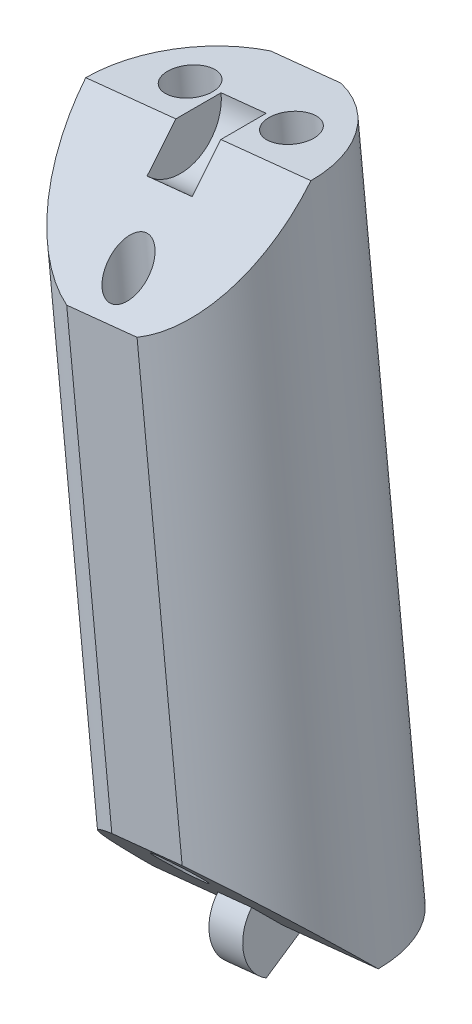
SolidWorks part; units mm, degrees
ref_plane "Front Plane" through (0, 0, 0) normal (0, 0, 1) x (1, 0, 0)
ref_plane "Top Plane" through (0, 0, 0) normal (0, 1, 0) x (1, 0, 0)
ref_plane "Right Plane" through (0, 0, 0) normal (1, 0, 0) x (0, 0, -1)
sketch "Sketch2" plane through (0, 0, 0) normal (0, 0, 1) x (1, 0, 0)
  line L0 (0, 0) -> (90, 0)
  line L1 (90, 0) -> (90, 120)
  line L2 (90, 120) -> (0, 120)
  line L3 (0, 120) -> (0, 0)
  line L4 (0, 120) -> (-10, 120)
  line L5 (-10, 120) -> (-10, 16.9491)
  line L6 (-10, 120) -> (57.5, 127)
  line L7 (57.5, 127) -> (90, 124)
  line L8 (90, 120) -> (99, 60)
  line L10 (90, 124) -> (90, 120)
  line L11 (5.9147, 0) -> (5.9147, -25)
  line L12 (5.9147, -25) -> (-4.0853, -25)
  line L13 (-4.0853, -29) -> (-4.0853, 0)
  line L14 (80, 0) -> (80, -25)
  line L15 (80, -25) -> (90, -25)
  line L16 (90, -29) -> (90, 0)
  line L17 (15.7927, 122.6748) -> (5.4776, 222.1414)
  line L18 (5.4776, 222.1414) -> (21.3923, 223.7918)
  line L19 (21.3923, 223.7918) -> (31.7073, 124.3252)
  line L20 (7.6492, 201.201) -> (23.5639, 202.8514)
  line L21 (10.9066, 169.7905) -> (26.8212, 171.441)
  line L22 (-10, 120) -> (-20.0396, 216.8108)
  line L23 (-20.0396, 216.8108) -> (-4.125, 218.4612)
  line L24 (-4.125, 218.4612) -> (5.9147, 121.6504)
  line L25 (-17.926, 196.4296) -> (-2.0114, 198.08)
  line L26 (-14.7556, 165.8578) -> (1.159, 167.5082)
  line L27 (57.5, 127) -> (46.9095, 229.1223)
  line L28 (46.9095, 229.1223) -> (30.9949, 227.4719)
  line L29 (30.9949, 227.4719) -> (41.5853, 125.3496)
  line L30 (33.2245, 205.9725) -> (49.1391, 207.6229)
  line L31 (36.5688, 173.7233) -> (52.4835, 175.3737)
  line L34 (90, 124) -> (99.1917, 223.5767)
  line L35 (99.1917, 223.5767) -> (83.2594, 225.0473)
  line L36 (83.2594, 225.0473) -> (74.0677, 125.4707)
  line L38 (81.3243, 204.0838) -> (97.2566, 202.6132)
  line L39 (78.4217, 172.6386) -> (94.354, 171.1679)
  line L40 (62.4078, 79.6749) -> (57.5, 127) construction
  line L41 (41.5853, 125.3496) -> (46.4931, 78.0244) construction
  line L42 (46.4931, 78.0244) -> (62.4078, 79.6749) construction
  line L43 (31.7073, 124.3252) -> (36.6151, 77.0001) construction
  line L44 (36.6151, 77.0001) -> (20.7005, 75.3496) construction
  line L45 (20.7005, 75.3496) -> (15.7927, 122.6748) construction
  line L46 (5.9147, 121.6504) -> (10.8224, 74.3253) construction
  line L47 (10.8224, 74.3253) -> (-5.0922, 72.6749) construction
  line L48 (-5.0922, 72.6749) -> (-10, 120) construction
  line L49 (74.0677, 125.4707) -> (69.6944, 78.0931) construction
  line L50 (69.6944, 78.0931) -> (85.7624, 78.0931) construction
  line L51 (85.7624, 78.0931) -> (90, 124) construction
  line L52 (-12.0823, 217.636) -> (10.4873, 0) construction
  line L53 (13.4349, 222.9666) -> (36.5574, 0) construction
  line L54 (38.9522, 228.2971) -> (62.6275, 0) construction
  line L55 (91.2256, 224.312) -> (70.5198, 0) construction
  line L59 (99, 60) -> (93.5277, 44.9649)
  line L60 (99, 60) -> (169.4769, 34.3485)
  line L61 (169.4769, 34.3485) -> (164.0046, 19.3134)
  line L62 (164.0046, 19.3134) -> (93.5277, 44.9649)
  line L63 (90, -2) -> (100, -2)
  line L64 (141.2862, 44.6091) -> (135.8138, 29.574)
  line L65 (99, 60) -> (55.7741, 75.7329) construction
  line L66 (55.7741, 75.7329) -> (50.3018, 60.6978) construction
  line L67 (100, -2) -> (100, -29)
  line L70 (-4.0853, -2) -> (-14.0853, -2)
  line L71 (-14.0853, -2) -> (-14.0853, -29)
  line L74 (-4.0853, 0) -> (0, 0)
  line L75 (-14.0853, -29) -> (-14.0853, -112.587)
  line L76 (-14.0853, -112.587) -> (100, -112.587)
  line L77 (100, -112.587) -> (100, -29)
  line L78 (-14.0853, -29) -> (100, -29)
  line L79 (-14.0853, -14.5) -> (100, -14.5) construction
  line L80 (31.7073, -112.587) -> (31.7073, -122.6232)
  line L81 (31.7073, -122.6232) -> (42.9573, -122.6232)
  line L82 (42.9573, -122.6232) -> (42.9573, -112.587)
  line L83 (-14.0853, -112.587) -> (-88.3667, -112.587)
  line L84 (-88.3667, -112.587) -> (-88.3667, -128.2699)
  line L85 (-88.3667, -128.2699) -> (169.4958, -128.2699)
  line L86 (169.4958, -128.2699) -> (169.4958, -112.587)
  line L87 (169.4958, -112.587) -> (100, -112.587)
  line L88 (90, 60) -> (-10, 60) construction
  line L89 (50.3018, 60.6978) -> (93.5277, 44.9649) construction
  line L90 (87.2806, 55.7521) -> (166.7408, 26.8309) construction
  line L91 (87.2806, 55.7521) -> (82.1749, 52.5336) construction
  line L92 (82.1749, 52.5336) -> (77.3257, 0) construction
  line L93 (83.1185, 56.6957) -> (86.337, 51.59) construction
  arc A0 (-10, 16.9491) -> (-4.0853, 0) centre (14.9876, 16.1624) ccw
  arc A1 (93.5277, 44.9649) -> (90, 0) centre (-126.4069, 39.5988) cw
  point P42 (41.1818, 206.7977)
  point P100 (84.7278, 54.1428)
  point P101 (84.7278, 54.1428)
  dimension "D11" = 47.3684
  dimension "D35" = 9
  dimension "D32" = 220
  dimension "D36" = 25
  dimension "D1" = 120
  dimension "D2" = 90
  dimension "D3" = 10
  dimension "D5" = 67.862
  dimension "D6" = 7
  dimension "D7" = 4
  dimension "D8" = 16
  dimension "D9" = 16
  dimension "D10" = 100
  dimension "D12" = 31.5789
  dimension "D13" = 16
  dimension "D14" = 16
  dimension "D15" = 16
  dimension "D16" = 25.7927
  dimension "D17" = 100
  dimension "D18" = 21.0526
  dimension "D19" = 31.5789
  dimension "D20" = 97.33
  dimension "D21" = 102.67
  dimension "D22" = 20.4905
  dimension "D23" = 30.7358
  dimension "D24" = 21.6147
  dimension "D25" = 32.4221
  dimension "D26" = 25
  dimension "D28" = 25
  dimension "D29" = 75
  dimension "D30" = 47.5789
  dimension "D31" = 30
  dimension "D33" = 46
  dimension "D34" = 20
  dimension "D37" = 2
  dimension "D38" = 2
  dimension "D39" = 27
  dimension "D40" = 10
  dimension "D41" = 10
  dimension "D42" = 27
  dimension "D43" = 14.5
  dimension "D44" = 127.5
ref_plane "Plane1" through (87.2806, 55.7521, 0) normal (-0.846, -0.5333, 0) x (0, 0, 1)
ref_plane "Plane2" through (82.1749, 52.5336, 0) normal (-0.0919, -0.9958, 0) x (-0.9958, 0.0919, 0)
ref_plane "Plane3" through (91.2256, 224.312, 0) normal (-0.0919, -0.9958, 0) x (-0.9958, 0.0919, 0)
ref_plane "Plane4" through (38.9522, 228.2971, 0) normal (0.1032, -0.9947, 0) x (-0.9947, -0.1032, 0)
ref_plane "Plane5" through (13.4349, 222.9666, 0) normal (0.1032, -0.9947, 0) x (-0.9947, -0.1032, 0)
ref_plane "Plane7" through (166.7408, 26.8309, 0) normal (0.9397, -0.342, 0) x (0, 0, -1)
ref_plane "Plane8" through (110.4217, -40.1902, 0) normal (0.9397, -0.342, 0) x (0, 0, -1)
ref_plane "Plane9" through (19.3664, 209.803, 0) normal (-0.0919, -0.9958, 0) x (-0.9958, 0.0919, 0)
ref_plane "Plane10" through (16.4638, 178.3578, 0) normal (-0.0919, -0.9958, 0) x (-0.9958, 0.0919, 0)
ref_plane "Plane11" through (-20.7793, 200.3721, 0) normal (0.1032, -0.9947, 0) x (-0.9947, -0.1032, 0)
ref_plane "Plane12" through (-17.435, 168.1229, 0) normal (0.1032, -0.9947, 0) x (-0.9947, -0.1032, 0)
ref_plane "Plane13" through (-20.5619, 198.2754, 0) normal (0.1032, -0.9947, 0) x (-0.9947, -0.1032, 0)
ref_plane "Plane14" through (-17.3045, 166.8649, 0) normal (0.1032, -0.9947, 0) x (-0.9947, -0.1032, 0)
ref_plane "Plane15" through (-12.0823, 217.636, 0) normal (0.1032, -0.9947, 0) x (-0.9947, -0.1032, 0)
ref_plane "Plane16" through (-20.3445, 196.1788, 0) normal (0.1032, -0.9947, 0) x (-0.9947, -0.1032, 0)
ref_plane "Plane17" through (-17.1741, 165.607, 0) normal (0.1032, -0.9947, 0) x (-0.9947, -0.1032, 0)
ref_plane "Plane18" through (12.1098, 131.1899, 0) normal (-0.0919, -0.9958, 0) x (-0.9958, 0.0919, 0)
ref_plane "Plane19" through (-12.4184, 119.7492, 0) normal (0.1032, -0.9947, 0) x (-0.9947, -0.1032, 0)
ref_plane "Plane20" through (0, 0, 0) normal (0, 0, 1) x (0.1032, -0.9947, 0)
ref_plane "Plane21" through (0, 0, 0) normal (0, 0, 1) x (-0.0919, -0.9958, 0)
ref_plane "Plane22" through (10.3758, 1.076, 0) normal (-0.9947, -0.1032, 0) x (0.1032, -0.9947, 0)
ref_plane "Plane23" through (36.1684, 3.7508, 0) normal (-0.9947, -0.1032, 0) x (0.1032, -0.9947, 0)
ref_plane "Plane24" through (61.9611, 6.4256, 0) normal (-0.9947, -0.1032, 0) x (0.1032, -0.9947, 0)
ref_plane "Plane25" through (69.924, -6.4545, 0) normal (-0.9958, 0.0919, 0) x (-0.0919, -0.9958, 0)
sketch "Sketch3" plane through (-20.3445, 196.1788, 0) normal (0.1032, -0.9947, 0) x (-0.9947, -0.1032, 0)
  line L0 (-2.4314, 0) -> (-18.4314, 0) construction
  circle A0 centre (-10.4314, 0) radius 8
  dimension "D1" = 16
extrude "Boss-Extrude1" add sketch "Sketch3" along normal blind 46.1037
sketch "Sketch4" plane through (10.3758, 1.076, 0) normal (-0.9947, -0.1032, 0) x (0.1032, -0.9947, 0)
  line L0 (-197.2309, 0) -> (-189.2309, 8)
  line L1 (-197.2309, 8) -> (-197.2309, -8) construction
  line L2 (-151.1272, 8) -> (-197.2309, 8) construction
  line L3 (-189.2309, 8) -> (-197.2309, 8)
  line L4 (-197.2309, 8) -> (-197.2309, 0)
  line L5 (-159.1272, 8) -> (-151.1272, 8)
  line L6 (-151.1272, 8) -> (-151.1272, 0)
  line L7 (-217.7214, 0) -> (1.0818, 0) construction
  line L8 (-151.1272, 0) -> (-159.1272, 8)
  dimension "D1" = 45
  dimension "D2" = 45
extrude "Cut-Extrude1" cut sketch "Sketch4" against normal through all and the other way through all
sketch "Sketch5" plane through (10.3758, 1.076, 0) normal (-0.9947, -0.1032, 0) x (0.1032, -0.9947, 0)
  line L1 (-151.1272, -2.8) -> (-148.7023, 1.4)
  line L6 (-151.1272, 0) -> (-159.1272, 8) construction
  line L11 (-151.1272, -8) -> (-151.1272, 0) construction
  line L12 (-153.1071, 1.9799) -> (-151.1272, 0)
  line L13 (-151.1272, 0) -> (-151.1272, -2.8)
  arc A3 (-153.1071, 1.9799) -> (-148.7023, 1.4) centre (-151.1272, 0) cw
  dimension "D2" = 2.8
  dimension "D1" = 30
  dimension "D3" = 2.8
extrude "Boss-Extrude2" add sketch "Sketch5" along normal mid plane 2.4
sketch "Sketch7" plane through (10.3758, 1.076, 0) normal (-0.9947, -0.1032, 0) x (0.1032, -0.9947, 0)
  line L6 (-197.2309, 0) -> (-197.2309, -8) construction
  line L7 (-189.2309, 8) -> (-197.2309, 0) construction
  line L8 (-194.9681, 2.2627) -> (-197.2309, 0)
  line L9 (-197.2309, 0) -> (-197.2309, -3.2)
  arc A1 (-197.2309, -3.2) -> (-194.9681, 2.2627) centre (-197.2309, 0) ccw
  dimension "D1" = 3.2
extrude "Cut-Extrude2" cut sketch "Sketch7" against normal mid plane 3.2
sketch "Sketch8" plane through (-20.3445, 196.1788, 0) normal (-0.1032, 0.9947, 0) x (0.9947, 0.1032, 0)
  line L0 (2.4314, 0) -> (18.4314, 0) construction
  circle A0 centre (10.4314, -5.5) radius 1.4
  circle A1 centre (6.8314, 3) radius 1.6
  circle A2 centre (14.0314, 3) radius 1.6
  point P9 (10.4314, 0)
  dimension "D1" = 3.2
  dimension "D2" = 3.2
  dimension "D3" = 2.8
  dimension "D4" = 3
  dimension "D5" = 5.5
  dimension "D6" = 3.6
  dimension "D7" = 3.6
  dimension "D8" = 3
extrude "Cut-Extrude3" cut sketch "Sketch8" against normal through all and the other way through all
sketch "Sketch9" plane through (-20.3445, 196.1788, 0) normal (-0.1032, 0.9947, 0) x (0.9947, 0.1032, 0)
  line L0 (7.9334, 7.6) -> (12.9294, 7.6)
  line L1 (-101.1265, 0) -> (155.3606, 0) construction
  line L2 (7.9334, -7.6) -> (12.9294, -7.6)
  arc A0 (18.4314, 0) -> (2.4314, 0) centre (10.4314, 0) ccw construction
  arc A1 (7.9334, 7.6) -> (12.9294, 7.6) centre (10.4314, 0) cw
  arc A2 (2.4314, 0) -> (18.4314, 0) centre (10.4314, 0) ccw construction
  arc A3 (7.9334, -7.6) -> (12.9294, -7.6) centre (10.4314, 0) ccw
  dimension "D1" = 7.6
  dimension "D2" = 7.6
extrude "Cut-Extrude4" cut sketch "Sketch9" against normal through all
